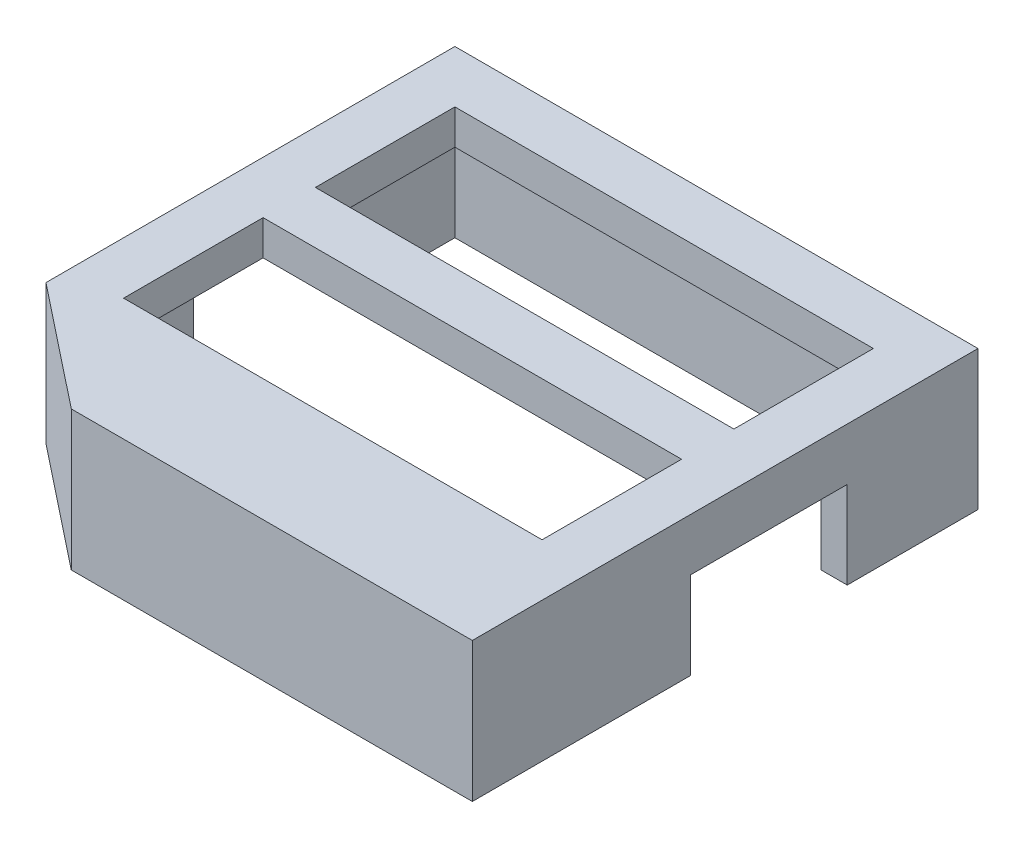
SolidWorks part; units mm, degrees
ref_plane "Front Plane" through (0, 0, 0) normal (0, 0, 1) x (1, 0, 0)
ref_plane "Top Plane" through (0, 0, 0) normal (0, 1, 0) x (1, 0, 0)
ref_plane "Right Plane" through (0, 0, 0) normal (1, 0, 0) x (0, 0, -1)
sketch "Sketch1" plane through (0, 0, 0) normal (0, 1, 0) x (1, 0, 0)
  line L1 (-29.2366, 0.9308) -> (0.7634, 0.9308)
  line L2 (-29.2366, 0.9308) -> (-29.2366, -28.0692)
  line L3 (-29.2366, -28.0692) -> (0.7634, -28.0692)
  line L4 (0.7634, 0.9308) -> (0.7634, -28.0692)
  dimension "D1" = 30
  dimension "D2" = 29
extrude "Boss-Extrude1" add sketch "Sketch1" along normal blind 8
sketch "Sketch2" plane through (0, 8, 0) normal (0, 1, 0) x (1, 0, 0)
  line L1 (-26.2366, -2.0692) -> (-2.2366, -2.0692)
  line L2 (-26.2366, -2.0692) -> (-26.2366, -10.0692)
  line L3 (-26.2366, -10.0692) -> (-2.2366, -10.0692)
  line L4 (-2.2366, -2.0692) -> (-2.2366, -10.0692)
  line L5 (-26.2366, -13.0692) -> (-2.2366, -13.0692)
  line L6 (-26.2366, -13.0692) -> (-26.2366, -21.0692)
  line L7 (-26.2366, -21.0692) -> (-2.2366, -21.0692)
  line L8 (-2.2366, -13.0692) -> (-2.2366, -21.0692)
  line L10 (0.7634, 0.9308) -> (-29.2366, 0.9308) construction
  line L11 (-29.2366, 0.9308) -> (-29.2366, -28.0692) construction
  line L12 (0.7634, -28.0692) -> (0.7634, 0.9308) construction
  dimension "D5" = 8
  dimension "D2" = 3
  dimension "D1" = 3
  dimension "D3" = 3
  dimension "D4" = 3
  dimension "D6" = 3
extrude "Cut-Extrude1" cut sketch "Sketch2" against normal blind 8
sketch "Sketch3" plane through (0, 8, 0) normal (0, 1, 0) x (1, 0, 0)
  line L0 (-29.2366, -22.5191) -> (-22.2366, -28.0692)
  line L1 (-29.2366, 0.9308) -> (-29.2366, -28.0692) construction
  line L2 (-29.2366, -28.0692) -> (0.7634, -28.0692) construction
  line L3 (-22.2366, -28.0692) -> (-29.2366, -28.0692)
  line L4 (-29.2366, -28.0692) -> (-29.2366, -22.5191)
  dimension "D1" = 3
  dimension "D2" = 7
extrude "Cut-Extrude2" cut sketch "Sketch3" against normal blind 8
sketch "cutout" plane through (0, 0, 0) normal (0, -1, 0) x (1, 0, 0)
  line L0 (-0.7366, 0.5692) -> (-27.7366, 0.5692)
  line L1 (-27.7366, 0.5692) -> (-27.7366, 21.7942)
  line L2 (-27.7366, 21.7942) -> (-21.7141, 26.5692)
  line L3 (-21.7141, 26.5692) -> (-0.7366, 26.5692)
  line L4 (-0.7366, 0.5692) -> (-0.7366, 26.5692)
  line L5 (0.7634, 28.0692) -> (0.7634, -0.9308) construction
  line L6 (-22.2366, 28.0692) -> (0.7634, 28.0692) construction
  line L7 (-22.2366, 28.0692) -> (-29.2366, 22.5191) construction
  line L8 (-29.2366, -0.9308) -> (-29.2366, 22.5191) construction
  line L9 (0.7634, -0.9308) -> (-29.2366, -0.9308) construction
  dimension "D1" = 1.5
  dimension "D2" = 1.5
  dimension "D3" = 1.5
  dimension "D4" = 1.5
  dimension "D5" = 1.5
extrude "Cut-Extrude3" cut sketch "cutout" against normal blind 6
sketch "belt_cutout" plane through (-29.2366, 0, 0) normal (-1, 0, 0) x (0, 0, 1)
  line L0 (-0.9308, 0) -> (22.5191, 0) construction
  line L1 (6.5692, 0) -> (15.5692, 0)
  line L2 (6.5692, 0) -> (6.5692, 5)
  line L3 (6.5692, 5) -> (15.5692, 5)
  line L4 (15.5692, 0) -> (15.5692, 5)
  line L5 (-0.9308, 8) -> (-0.9308, 0) construction
  dimension "D1" = 9
  dimension "D2" = 5
  dimension "D3" = 7.5
extrude "Cut-Extrude4" cut sketch "belt_cutout" against normal blind 30
equation "\"buckle_thickness\"= 8"
equation "\"visable_border\"= 3"
equation "\"cutout_border\"= 1.5"
equation "\"belt_thickness\"= 9"
equation "\"belt_width\"= 5"
equation "\"D1@belt_cutout\" = \"belt_thickness\""
equation "\"D2@belt_cutout\" = \"belt_width\""
equation "\"belt_placement\"= 7.5"
equation "\"D3@belt_cutout\" = \"belt_placement\""
equation "\"D1@cutout\" = \"cutout_border\""
equation "\"D2@cutout\" = \"cutout_border\""
equation "\"D3@cutout\" = \"cutout_border\""
equation "\"D4@cutout\" = \"cutout_border\""
equation "\"D5@cutout\" = \"cutout_border\""
equation "\"D2@Sketch2\"=\"visable_border\""
equation "\"D1@Sketch2\"=\"visable_border\""
equation "\"D3@Sketch2\"=\"visable_border\""
equation "\"D4@Sketch2\"=\"visable_border\""
equation "\"D6@Sketch2\"=\"visable_border\""
equation "\"base_size\"= 30"
equation "\"D1@Sketch1\"=\"base_size\""
